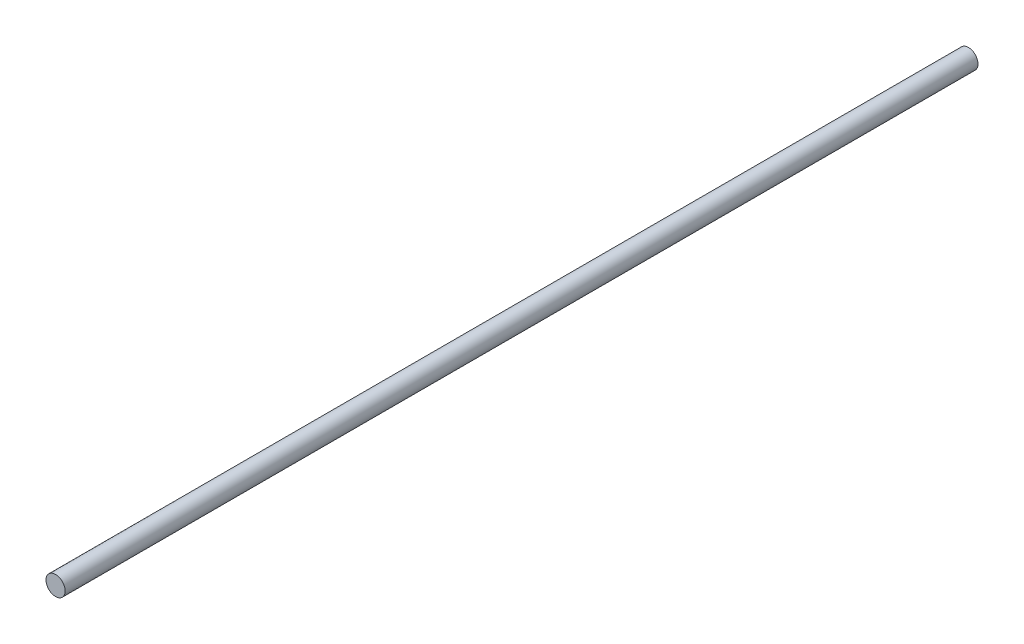
SolidWorks part; units mm, degrees
ref_plane "Front Plane" through (0, 0, 0) normal (0, 0, 1) x (1, 0, 0)
ref_plane "Top Plane" through (0, 0, 0) normal (0, 1, 0) x (1, 0, 0)
ref_plane "Right Plane" through (0, 0, 0) normal (1, 0, 0) x (0, 0, -1)
sketch "Sketch1" plane through (0, 0, 0) normal (0, 0, 1) x (1, 0, 0)
  circle A0 centre (0, 0) radius 4
extrude "Boss-Extrude1" add sketch "Sketch1" along normal blind 381
